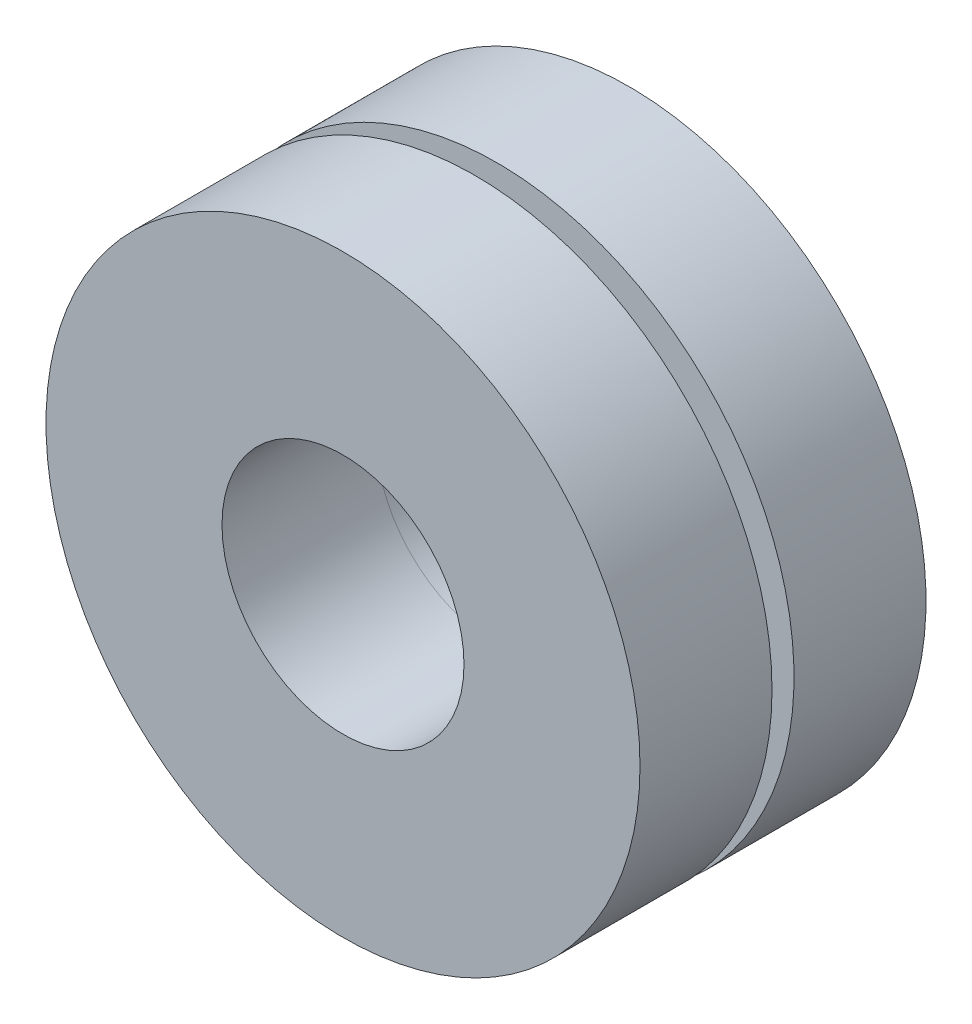
SolidWorks part; units mm, degrees
ref_plane "Front Plane" through (0, 0, 0) normal (0, 0, 1) x (1, 0, 0)
ref_plane "Top Plane" through (0, 0, 0) normal (0, 1, 0) x (1, 0, 0)
ref_plane "Right Plane" through (0, 0, 0) normal (1, 0, 0) x (0, 0, -1)
sketch "Sketch1" plane through (0, 0, 0) normal (0, 0, 1) x (1, 0, 0)
  circle A0 centre (0, 0) radius 2.794
  circle A1 centre (0, 0) radius 4.572
  dimension "D1" = 1.778
  dimension "D2" = 5.588
extrude "Boss-Extrude2" add sketch "Sketch1" along normal blind 0.508 contours A1
sketch "Sketch3" plane through (0, 0, 0.508) normal (0, 0, 1) x (1, 0, 0)
  circle A0 centre (0, 0) radius 2.794
  circle A1 centre (0, 0) radius 6.858
  dimension "D1" = 4.064
  dimension "D2" = 5.588
extrude "Boss-Extrude3" add sketch "Sketch3" along normal blind 3.048
sketch "Sketch4" plane through (0, 0, 0) normal (0, 0, -1) x (-1, 0, 0)
  circle A0 centre (0, 0) radius 2.794
  circle A1 centre (0, 0) radius 6.858
  dimension "D1" = 5.588
extrude "Boss-Extrude4" add sketch "Sketch4" along normal blind 3.048 separate body
